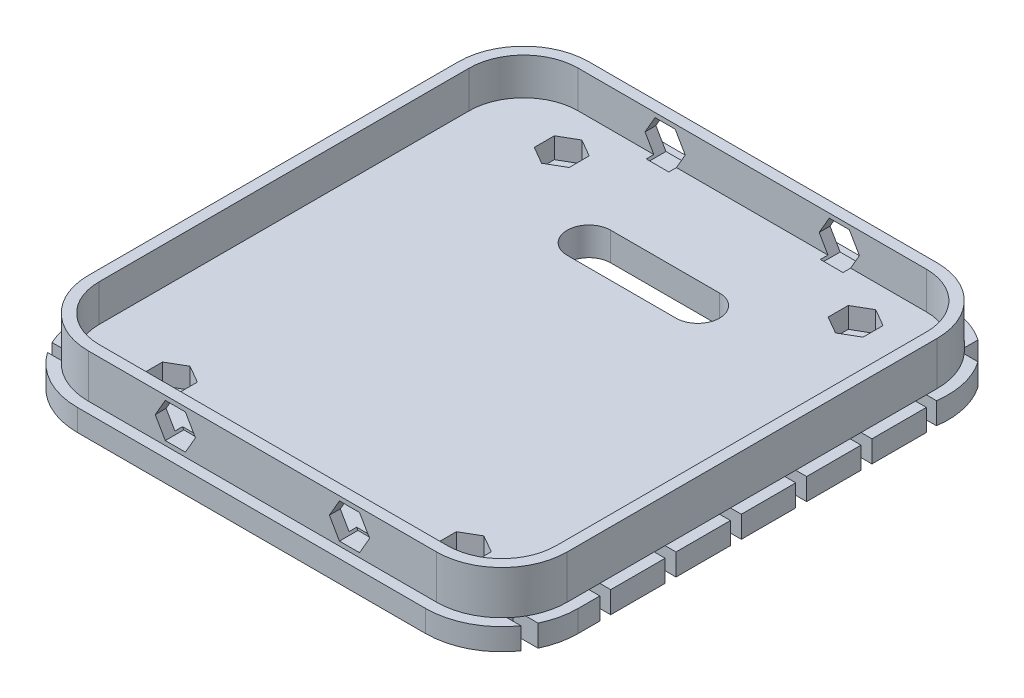
SolidWorks part; units mm, degrees
ref_plane "Front Plane" through (0, 0, 0) normal (0, 0, 1) x (1, 0, 0)
ref_plane "Top Plane" through (0, 0, 0) normal (0, 1, 0) x (1, 0, 0)
ref_plane "Right Plane" through (0, 0, 0) normal (1, 0, 0) x (0, 0, -1)
sketch "Sketch1" plane through (0, 0, 0) normal (0, 1, 0) x (1, 0, 0)
  line L1 (0, 0) -> (220, 0)
  line L2 (0, 0) -> (0, 230)
  line L3 (0, 230) -> (220, 230)
  line L4 (220, 0) -> (220, 230)
  dimension "D1" = 230
  dimension "D2" = 220
extrude "Boss-Extrude1" add sketch "Sketch1" along normal blind 20
sketch "Sketch3" plane through (0, 20, 0) normal (0, 1, 0) x (1, 0, 0)
  line L0 (110, 230) -> (110, 0) construction
  line L1 (0, 230) -> (15, 230)
  line L2 (0, 230) -> (0, 215)
  line L3 (0, 215) -> (15, 215)
  line L4 (15, 230) -> (15, 215)
  line L5 (220, 230) -> (0, 230) construction
  line L6 (0, 0) -> (220, 0) construction
  line L7 (0, 115) -> (220, 115) construction
  line L8 (0, 230) -> (0, 0) construction
  line L9 (220, 0) -> (220, 230) construction
  line L10 (0, 215) -> (0, 200)
  line L11 (0, 215) -> (15, 215)
  line L12 (15, 215) -> (15, 200)
  line L13 (0, 200) -> (15, 200)
  line L14 (0, 200) -> (0, 185)
  line L15 (0, 200) -> (15, 200)
  line L16 (15, 200) -> (15, 185)
  line L17 (0, 185) -> (15, 185)
  line L18 (0, 185) -> (0, 170)
  line L19 (0, 185) -> (15, 185)
  line L20 (15, 185) -> (15, 170)
  line L21 (0, 170) -> (15, 170)
  line L22 (0, 170) -> (0, 155)
  line L23 (0, 170) -> (15, 170)
  line L24 (15, 170) -> (15, 155)
  line L25 (0, 155) -> (15, 155)
  line L26 (0, 155) -> (0, 140)
  line L27 (0, 155) -> (15, 155)
  line L28 (15, 155) -> (15, 140)
  line L29 (0, 140) -> (15, 140)
  line L30 (0, 140) -> (0, 125)
  line L31 (0, 140) -> (15, 140)
  line L32 (15, 140) -> (15, 125)
  line L33 (0, 125) -> (15, 125)
  line L34 (0, 125) -> (0, 110)
  line L35 (0, 125) -> (15, 125)
  line L36 (15, 125) -> (15, 110)
  line L37 (0, 110) -> (15, 110)
  line L38 (0, 110) -> (0, 95)
  line L39 (0, 110) -> (15, 110)
  line L40 (15, 110) -> (15, 95)
  line L41 (0, 95) -> (15, 95)
  line L42 (0, 95) -> (0, 80)
  line L43 (0, 95) -> (15, 95)
  line L44 (15, 95) -> (15, 80)
  line L45 (0, 80) -> (15, 80)
  line L46 (0, 80) -> (0, 65)
  line L47 (0, 80) -> (15, 80)
  line L48 (15, 80) -> (15, 65)
  line L49 (0, 65) -> (15, 65)
  line L50 (0, 65) -> (0, 50)
  line L51 (0, 65) -> (15, 65)
  line L52 (15, 65) -> (15, 50)
  line L53 (0, 50) -> (15, 50)
  line L54 (0, 50) -> (0, 35)
  line L55 (0, 50) -> (15, 50)
  line L56 (15, 50) -> (15, 35)
  line L57 (0, 35) -> (15, 35)
  line L58 (0, 35) -> (0, 20)
  line L59 (0, 35) -> (15, 35)
  line L60 (15, 35) -> (15, 20)
  line L61 (0, 20) -> (15, 20)
  line L62 (0, 20) -> (0, 5)
  line L63 (0, 20) -> (15, 20)
  line L64 (15, 20) -> (15, 5)
  line L65 (0, 5) -> (15, 5)
  line L66 (220, 5) -> (205, 5)
  line L67 (205, 20) -> (205, 5)
  line L68 (220, 20) -> (205, 20)
  line L69 (220, 20) -> (220, 5)
  line L70 (220, 20) -> (205, 20)
  line L71 (205, 35) -> (205, 20)
  line L72 (220, 35) -> (205, 35)
  line L73 (220, 35) -> (220, 20)
  line L74 (220, 35) -> (205, 35)
  line L75 (205, 50) -> (205, 35)
  line L76 (220, 50) -> (205, 50)
  line L77 (220, 50) -> (220, 35)
  line L78 (220, 50) -> (205, 50)
  line L79 (205, 65) -> (205, 50)
  line L80 (220, 65) -> (205, 65)
  line L81 (220, 65) -> (220, 50)
  line L82 (220, 65) -> (205, 65)
  line L83 (205, 80) -> (205, 65)
  line L84 (220, 80) -> (205, 80)
  line L85 (220, 80) -> (220, 65)
  line L86 (220, 80) -> (205, 80)
  line L87 (205, 95) -> (205, 80)
  line L88 (220, 95) -> (205, 95)
  line L89 (220, 95) -> (220, 80)
  line L90 (220, 95) -> (205, 95)
  line L91 (205, 110) -> (205, 95)
  line L92 (220, 110) -> (205, 110)
  line L93 (220, 110) -> (220, 95)
  line L94 (220, 110) -> (205, 110)
  line L95 (205, 125) -> (205, 110)
  line L96 (220, 125) -> (205, 125)
  line L97 (220, 125) -> (220, 110)
  line L98 (220, 125) -> (205, 125)
  line L99 (205, 140) -> (205, 125)
  line L100 (220, 140) -> (205, 140)
  line L101 (220, 140) -> (220, 125)
  line L102 (220, 140) -> (205, 140)
  line L103 (205, 155) -> (205, 140)
  line L104 (220, 155) -> (205, 155)
  line L105 (220, 155) -> (220, 140)
  line L106 (220, 155) -> (205, 155)
  line L107 (205, 170) -> (205, 155)
  line L108 (220, 170) -> (205, 170)
  line L109 (220, 170) -> (220, 155)
  line L110 (220, 170) -> (205, 170)
  line L111 (205, 185) -> (205, 170)
  line L112 (220, 185) -> (205, 185)
  line L113 (220, 185) -> (220, 170)
  line L114 (220, 185) -> (205, 185)
  line L115 (205, 200) -> (205, 185)
  line L116 (220, 200) -> (205, 200)
  line L117 (220, 200) -> (220, 185)
  line L118 (220, 200) -> (205, 200)
  line L119 (205, 215) -> (205, 200)
  line L120 (220, 215) -> (205, 215)
  line L121 (220, 215) -> (220, 200)
  line L122 (205, 230) -> (205, 215)
  line L123 (220, 215) -> (205, 215)
  line L124 (220, 230) -> (220, 215)
  line L125 (220, 230) -> (205, 230)
  dimension "D1" = 15
  dimension "D2" = 15
  dimension "D3" = 15
fillet "Fillet1" radius 30 4 edges at (0, 10, 0) (220, 10, 0) (220, 10, -230) (0, 10, -230)
sketch "Sketch4" plane through (0, 0, 0) normal (0, -1, 0) x (-1, 0, 0)
  line L60 (-210, 10) -> (-218.7228, 10)
  line L61 (-210, 10) -> (-218.7228, 10)
  line L62 (-1.2772, 10) -> (-10, 10)
  line L63 (-1.2772, 10) -> (-10, 10)
  line L232 (-225, 40) -> (-225, 30)
  line L233 (-221.6228, 15) -> (-210, 15)
  line L234 (-210, 15) -> (-210, 10)
  line L235 (-190, -5) -> (-30, -5)
  line L236 (-10, 10) -> (-10, 15)
  line L237 (-10, 15) -> (1.6228, 15)
  line L238 (5, 105) -> (5, 130)
  line L239 (5, 190) -> (-10, 190)
  line L240 (-1.2772, 220) -> (-10, 220)
  line L241 (-10, 220) -> (-10, 228.7228)
  line L242 (-30, 235) -> (-190, 235)
  line L243 (-210, 228.7228) -> (-210, 220)
  line L244 (-210, 220) -> (-218.7228, 220)
  line L245 (-210, 190) -> (-225, 190)
  line L246 (-225, 40) -> (-225, 30)
  line L247 (-221.6228, 15) -> (-210, 15)
  line L248 (-210, 15) -> (-210, 10)
  line L249 (-190, -5) -> (-30, -5)
  line L250 (-10, 10) -> (-10, 15)
  line L251 (-10, 15) -> (1.6228, 15)
  line L252 (5, 105) -> (5, 130)
  line L253 (5, 190) -> (-10, 190)
  line L254 (-1.2772, 220) -> (-10, 220)
  line L255 (-10, 220) -> (-10, 228.7228)
  line L256 (-30, 235) -> (-190, 235)
  line L257 (-210, 228.7228) -> (-210, 220)
  line L258 (-210, 220) -> (-218.7228, 220)
  line L259 (-210, 190) -> (-225, 190)
  line L260 (-210, 165) -> (-210, 160)
  line L262 (-210, 165) -> (-210, 160)
  line L264 (-210, 160) -> (-225, 160)
  line L266 (-210, 160) -> (-225, 160)
  line L268 (-225, 160) -> (-225, 135)
  line L270 (-225, 160) -> (-225, 135)
  line L272 (-225, 135) -> (-210, 135)
  line L274 (-225, 135) -> (-210, 135)
  line L276 (-210, 135) -> (-210, 130)
  line L278 (-210, 135) -> (-210, 130)
  line L280 (-210, 130) -> (-225, 130)
  line L282 (-210, 130) -> (-225, 130)
  line L284 (-225, 130) -> (-225, 105)
  line L286 (-225, 130) -> (-225, 105)
  line L288 (-225, 105) -> (-210, 105)
  line L290 (-225, 105) -> (-210, 105)
  line L292 (-210, 105) -> (-210, 100)
  line L294 (-210, 105) -> (-210, 100)
  line L296 (-210, 100) -> (-225, 100)
  line L298 (-210, 100) -> (-225, 100)
  line L300 (-225, 100) -> (-225, 75)
  line L302 (-225, 100) -> (-225, 75)
  line L304 (-225, 75) -> (-210, 75)
  line L306 (-225, 75) -> (-210, 75)
  line L308 (-210, 75) -> (-210, 70)
  line L310 (-210, 75) -> (-210, 70)
  line L312 (-210, 70) -> (-225, 70)
  line L314 (-210, 70) -> (-225, 70)
  line L316 (-225, 70) -> (-225, 45)
  line L318 (-225, 70) -> (-225, 45)
  line L320 (-225, 45) -> (-210, 45)
  line L322 (-225, 45) -> (-210, 45)
  line L324 (-210, 45) -> (-210, 40)
  line L326 (-210, 45) -> (-210, 40)
  line L328 (-210, 40) -> (-225, 40)
  line L330 (-210, 40) -> (-225, 40)
  line L332 (5, 30) -> (5, 40)
  line L334 (5, 30) -> (5, 40)
  line L336 (5, 40) -> (-10, 40)
  line L338 (5, 40) -> (-10, 40)
  line L340 (-10, 40) -> (-10, 45)
  line L342 (-10, 40) -> (-10, 45)
  line L344 (-10, 45) -> (5, 45)
  line L346 (-10, 45) -> (5, 45)
  line L348 (5, 45) -> (5, 70)
  line L349 (5, 45) -> (5, 70)
  line L350 (5, 70) -> (-10, 70)
  line L351 (5, 70) -> (-10, 70)
  line L352 (-10, 70) -> (-10, 75)
  line L353 (-10, 70) -> (-10, 75)
  line L354 (-10, 75) -> (5, 75)
  line L355 (-10, 75) -> (5, 75)
  line L356 (5, 75) -> (5, 100)
  line L357 (5, 75) -> (5, 100)
  line L358 (5, 100) -> (-10, 100)
  line L359 (5, 100) -> (-10, 100)
  line L360 (-10, 100) -> (-10, 105)
  line L361 (-10, 100) -> (-10, 105)
  line L362 (-10, 105) -> (5, 105)
  line L363 (-10, 105) -> (5, 105)
  line L364 (5, 130) -> (-10, 130)
  line L365 (5, 130) -> (-10, 130)
  line L366 (-10, 130) -> (-10, 135)
  line L367 (-10, 130) -> (-10, 135)
  line L368 (-10, 135) -> (5, 135)
  line L369 (-10, 135) -> (5, 135)
  line L370 (5, 135) -> (5, 160)
  line L371 (5, 135) -> (5, 160)
  line L372 (5, 160) -> (-10, 160)
  line L373 (5, 160) -> (-10, 160)
  line L374 (-10, 160) -> (-10, 165)
  line L375 (-10, 160) -> (-10, 165)
  line L376 (-10, 165) -> (5, 165)
  line L377 (-10, 165) -> (5, 165)
  line L378 (5, 165) -> (5, 190)
  line L379 (5, 165) -> (5, 190)
  line L380 (-10, 190) -> (-10, 195)
  line L381 (-10, 190) -> (-10, 195)
  line L382 (-10, 195) -> (4.641, 195)
  line L383 (-10, 195) -> (4.641, 195)
  line L384 (-224.641, 195) -> (-210, 195)
  line L385 (-224.641, 195) -> (-210, 195)
  line L386 (-210, 195) -> (-210, 190)
  line L387 (-210, 195) -> (-210, 190)
  line L388 (-225, 190) -> (-225, 165)
  line L389 (-225, 190) -> (-225, 165)
  line L390 (-225, 165) -> (-210, 165)
  line L391 (-225, 165) -> (-210, 165)
  arc A32 (-225, 30) -> (-221.6228, 15) centre (-190, 30) ccw
  arc A33 (-218.7228, 10) -> (-190, -5) centre (-190, 30) ccw
  arc A34 (-30, -5) -> (-1.2772, 10) centre (-30, 30) ccw
  arc A35 (1.6228, 15) -> (5, 30) centre (-30, 30) ccw
  arc A36 (4.641, 195) -> (-1.2772, 220) centre (-30, 200) ccw
  arc A37 (-10, 228.7228) -> (-30, 235) centre (-30, 200) ccw
  arc A38 (-190, 235) -> (-210, 228.7228) centre (-190, 200) ccw
  arc A39 (-218.7228, 220) -> (-224.641, 195) centre (-190, 200) ccw
  arc A40 (-225, 30) -> (-221.6228, 15) centre (-190, 30) ccw
  arc A41 (-218.7228, 10) -> (-190, -5) centre (-190, 30) ccw
  arc A42 (-30, -5) -> (-1.2772, 10) centre (-30, 30) ccw
  arc A43 (1.6228, 15) -> (5, 30) centre (-30, 30) ccw
  arc A44 (4.641, 195) -> (-1.2772, 220) centre (-30, 200) ccw
  arc A45 (-10, 228.7228) -> (-30, 235) centre (-30, 200) ccw
  arc A46 (-190, 235) -> (-210, 228.7228) centre (-190, 200) ccw
  arc A47 (-218.7228, 220) -> (-224.641, 195) centre (-190, 200) ccw
  dimension "D1" = 5
extrude "Boss-Extrude4" add sketch "Sketch4" along normal blind 10
sketch "Sketch20" plane through (0, 20, 0) normal (0, 1, 0) x (1, 0, 0)
  line L4 (215, 30) -> (215, 200)
  line L5 (215, 30) -> (215, 200)
  line L6 (5, 200) -> (5, 30)
  line L7 (5, 200) -> (5, 30)
  line L116 (190, 225) -> (30, 225)
  line L118 (30, 5) -> (190, 5)
  line L120 (190, 225) -> (30, 225)
  line L122 (30, 5) -> (190, 5)
  arc A4 (215, 200) -> (190, 225) centre (190, 200) ccw
  arc A5 (215, 200) -> (190, 225) centre (190, 200) ccw
  arc A6 (5, 30) -> (30, 5) centre (30, 30) ccw
  arc A7 (5, 30) -> (30, 5) centre (30, 30) ccw
  arc A17 (30, 225) -> (5, 200) centre (30, 200) ccw
  arc A19 (190, 5) -> (215, 30) centre (190, 30) ccw
  arc A21 (30, 225) -> (5, 200) centre (30, 200) ccw
  arc A23 (190, 5) -> (215, 30) centre (190, 30) ccw
  dimension "D1" = 5
extrude "Cut-Extrude10" cut sketch "Sketch20" against normal blind 17
sketch "Sketch7" plane through (0, -10, 0) normal (0, -1, 0) x (-1, 0, 0)
  line L0 (-110, -5) -> (-110, 235) construction
  line L1 (-42.5, 115) -> (-177.5, 115) construction
  line L3 (-190, -5) -> (-30, -5) construction
  line L4 (-42.5, 25) -> (-177.5, 25)
  line L5 (-42.5, 25) -> (-42.5, 205)
  line L6 (-42.5, 205) -> (-177.5, 205)
  line L7 (-177.5, 25) -> (-177.5, 205)
  line L8 (-30, 235) -> (-190, 235) construction
  line L9 (5, 105) -> (5, 130) construction
  circle A0 centre (-42.5, 25) radius 5
  circle A1 centre (-177.5, 25) radius 5
  circle A2 centre (-177.5, 205) radius 5
  circle A3 centre (-42.5, 205) radius 5
  dimension "D7" = 10
  dimension "D1" = 180
  dimension "D2" = 30
  dimension "D3" = 30
  dimension "D4" = 47.5
  dimension "D6" = 135
extrude "Cut-Extrude3" cut sketch "Sketch7" against normal through all contours A2 | A3 | A0 | A1
sketch "Sketch8" plane through (0, 0, -230) normal (0, 0, -1) x (-1, 0, 0)
  line L0 (-110, 20) -> (-110, 0) construction
  line L1 (-190, 20) -> (-30, 20) construction
  line L2 (-30, 0) -> (-190, 0) construction
  line L3 (-190, 10) -> (-30, 10) construction
  line L4 (-190, 20) -> (-190, 0) construction
  line L5 (-30, 0) -> (-30, 20) construction
  circle A0 centre (-150, 10) radius 5
  circle A1 centre (-70, 10) radius 5
  dimension "D1" = 10
  dimension "D2" = 40
sketch "Sketch13" plane through (0, 0, 0) normal (0, 0, 1) x (1, 0, 0)
  circle A0 centre (70, 10) radius 5
  circle A1 centre (150, 10) radius 5
extrude "Cut-Extrude4" cut sketch "Sketch8" against normal blind 30
extrude "Cut-Extrude5" cut sketch "Sketch13" against normal blind 30
sketch "Sketch16" plane through (0, 0, -230) normal (0, 0, -1) x (-1, 0, 0)
  line L0 (-110, 20) -> (-110, 0) construction
  line L1 (-159.2376, 10) -> (-154.6188, 2)
  line L2 (-154.6188, 2) -> (-145.3812, 2)
  line L3 (-145.3812, 2) -> (-140.7624, 10)
  line L4 (-140.7624, 10) -> (-145.3812, 18)
  line L5 (-145.3812, 18) -> (-154.6188, 18)
  line L6 (-154.6188, 18) -> (-159.2376, 10)
  line L7 (-190, 20) -> (-30, 20) construction
  line L8 (-30, 0) -> (-190, 0) construction
  line L9 (-65.3812, 18) -> (-60.7624, 10)
  line L10 (-74.6188, 18) -> (-65.3812, 18)
  line L11 (-79.2376, 10) -> (-74.6188, 18)
  line L12 (-74.6188, 2) -> (-79.2376, 10)
  line L13 (-65.3812, 2) -> (-74.6188, 2)
  line L14 (-60.7624, 10) -> (-65.3812, 2)
  circle A0 centre (-150, 10) radius 8 construction
  circle A1 centre (-70, 10) radius 8 construction
  dimension "D1" = 16
sketch "Sketch17" plane through (0, 0, 0) normal (0, 0, 1) x (1, 0, 0)
  line L0 (110, 20) -> (110, 0) construction
  line L1 (60.7624, 10) -> (65.3812, 2)
  line L2 (65.3812, 2) -> (74.6188, 2)
  line L3 (74.6188, 2) -> (79.2376, 10)
  line L4 (79.2376, 10) -> (74.6188, 18)
  line L5 (74.6188, 18) -> (65.3812, 18)
  line L6 (65.3812, 18) -> (60.7624, 10)
  line L7 (154.6188, 18) -> (159.2376, 10)
  line L8 (145.3812, 18) -> (154.6188, 18)
  line L9 (140.7624, 10) -> (145.3812, 18)
  line L10 (145.3812, 2) -> (140.7624, 10)
  line L11 (154.6188, 2) -> (145.3812, 2)
  line L12 (159.2376, 10) -> (154.6188, 2)
  circle A0 centre (70, 10) radius 8 construction
  circle A1 centre (150, 10) radius 8 construction
extrude "Cut-Extrude6" cut sketch "Sketch17" against normal blind 8.5
extrude "Cut-Extrude7" cut sketch "Sketch16" against normal blind 8.5
sketch "Sketch18" plane through (0, 20, 0) normal (0, 1, 0) x (1, 0, 0)
  line L0 (110, 230) -> (110, 0) construction
  line L1 (42.5, 195.7624) -> (50.5, 200.3812)
  line L2 (50.5, 200.3812) -> (50.5, 209.6188)
  line L3 (50.5, 209.6188) -> (42.5, 214.2376)
  line L4 (42.5, 214.2376) -> (34.5, 209.6188)
  line L5 (34.5, 209.6188) -> (34.5, 200.3812)
  line L6 (34.5, 200.3812) -> (42.5, 195.7624)
  line L7 (190, 230) -> (30, 230) construction
  line L8 (30, 0) -> (190, 0) construction
  line L9 (110, 115) -> (241.1104, 115) construction
  line L10 (241.1104, 115) -> (-52.3186, 115) construction
  line L11 (185.5, 200.3812) -> (177.5, 195.7624)
  line L12 (185.5, 209.6188) -> (185.5, 200.3812)
  line L13 (177.5, 214.2376) -> (185.5, 209.6188)
  line L14 (169.5, 209.6188) -> (177.5, 214.2376)
  line L15 (169.5, 200.3812) -> (169.5, 209.6188)
  line L16 (177.5, 195.7624) -> (169.5, 200.3812)
  line L17 (185.5, 20.3812) -> (185.5, 29.6188)
  line L18 (177.5, 15.7624) -> (185.5, 20.3812)
  line L19 (169.5, 20.3812) -> (177.5, 15.7624)
  line L20 (169.5, 29.6188) -> (169.5, 20.3812)
  line L21 (177.5, 34.2376) -> (169.5, 29.6188)
  line L22 (185.5, 29.6188) -> (177.5, 34.2376)
  line L23 (34.5, 29.6188) -> (42.5, 34.2376)
  line L24 (34.5, 20.3812) -> (34.5, 29.6188)
  line L25 (42.5, 15.7624) -> (34.5, 20.3812)
  line L26 (50.5, 20.3812) -> (42.5, 15.7624)
  line L27 (50.5, 29.6188) -> (50.5, 20.3812)
  line L28 (42.5, 34.2376) -> (50.5, 29.6188)
  circle A0 centre (42.5, 205) radius 8 construction
  circle A1 centre (177.5, 205) radius 8 construction
  circle A2 centre (177.5, 25) radius 8 construction
  circle A3 centre (42.5, 25) radius 8 construction
  point P17 (177.5, 205)
  point P27 (42.5, 25)
  point P28 (177.5, 25)
  dimension "D1" = 16
extrude "Cut-Extrude8" cut sketch "Sketch18" against normal blind 26.5
sketch "Sketch19" plane through (0, 20, 0) normal (0, 1, 0) x (1, 0, 0)
  line L0 (110, 0) -> (110, 230) construction
  line L1 (30, 0) -> (190, 0) construction
  line L2 (190, 230) -> (30, 230) construction
  line L3 (110, 115) -> (0, 115) construction
  line L4 (0, 200) -> (0, 30) construction
  line L5 (110, 115) -> (220, 115) construction
  line L6 (220, 30) -> (220, 200) construction
  line L7 (110, 175) -> (220, 175) construction
  line L8 (85, 175) -> (135, 175) construction
  line L9 (85, 185) -> (135, 185)
  line L10 (85, 165) -> (135, 165)
  arc A0 (85, 185) -> (85, 165) centre (85, 175) ccw
  arc A1 (135, 165) -> (135, 185) centre (135, 175) ccw
  point P17 (110, 175)
  dimension "D2" = 10
  dimension "D3" = 50
  dimension "D1" = 60
extrude "Cut-Extrude9" cut sketch "Sketch19" against normal through all
